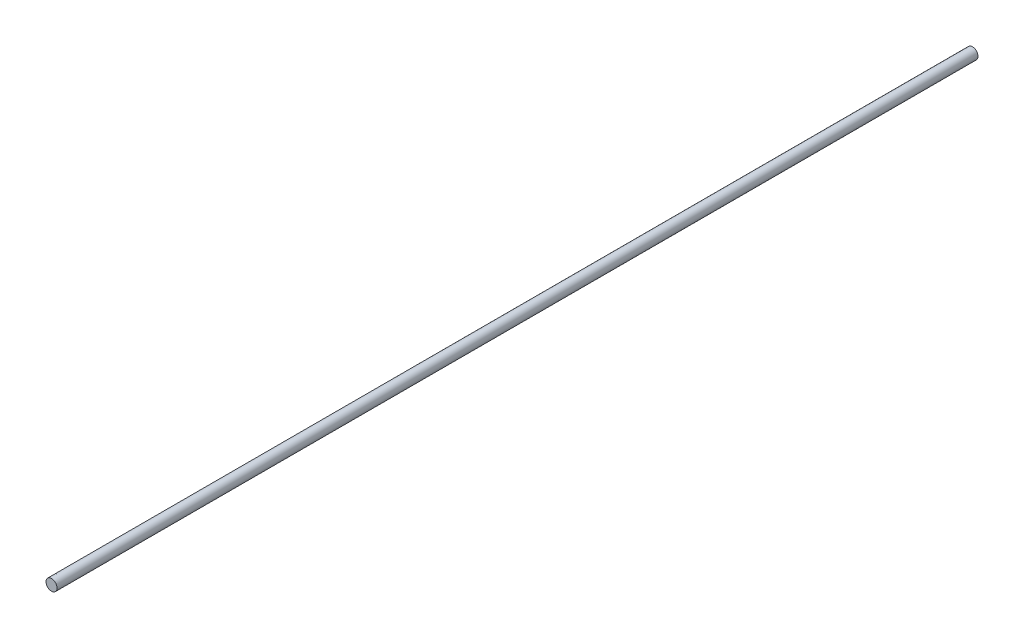
SolidWorks part; units mm, degrees
ref_plane "Front Plane" through (0, 0, 0) normal (0, 0, 1) x (1, 0, 0)
ref_plane "Top Plane" through (0, 0, 0) normal (0, 1, 0) x (1, 0, 0)
ref_plane "Right Plane" through (0, 0, 0) normal (1, 0, 0) x (0, 0, -1)
sketch "Sketch1" plane through (0, 0, 0) normal (0, 0, 1) x (1, 0, 0)
  circle A0 centre (0, 0) radius 6
  dimension "D1" = 12
extrude "Boss-Extrude2" add sketch "Sketch1" along normal blind 1000
